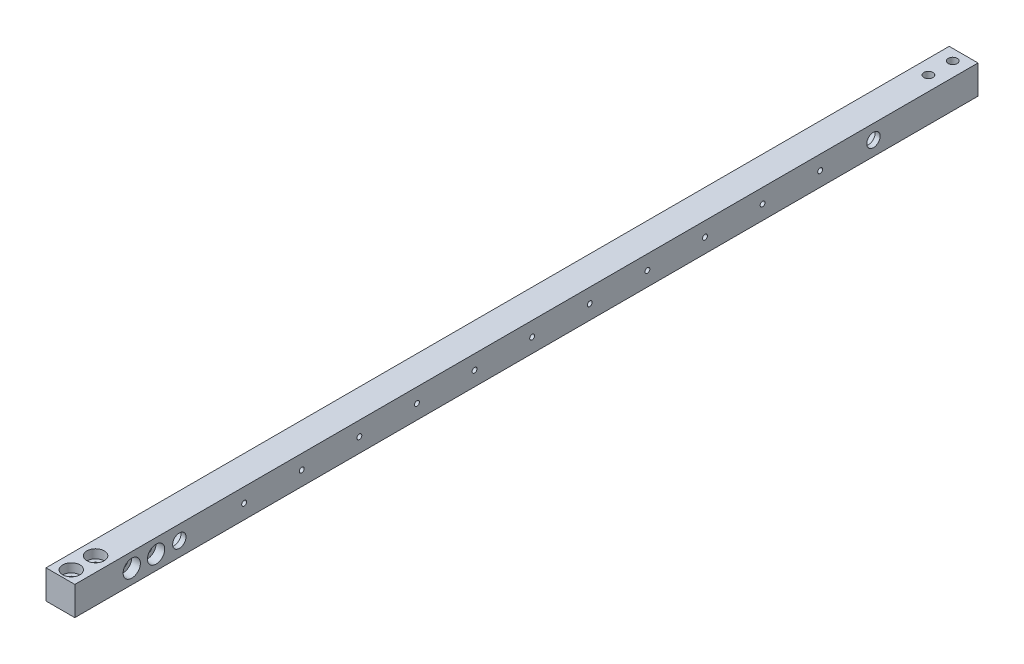
SolidWorks part; units mm, degrees
ref_plane "Front Plane" through (0, 0, 0) normal (0, 0, 1) x (1, 0, 0)
ref_plane "Top Plane" through (0, 0, 0) normal (0, 1, 0) x (1, 0, 0)
ref_plane "Right Plane" through (0, 0, 0) normal (1, 0, 0) x (0, 0, -1)
sketch "Sketch1" plane through (0, 0, 0) normal (0, 0, 1) x (1, 0, 0)
  line L1 (0, 0) -> (15.875, 0)
  line L2 (0, 0) -> (0, 15.875)
  line L3 (0, 15.875) -> (15.875, 15.875)
  line L4 (15.875, 0) -> (15.875, 15.875)
  dimension "D1" = 15.875
  dimension "D2" = 15.875
extrude "Boss-Extrude1" add sketch "Sketch1" along normal blind 497.84
sketch "Sketch8" plane through (0, 0, 0) normal (-1, 0, 0) x (0, 0, 1)
  line L0 (0, 15.875) -> (0, 0) construction
  line L1 (497.84, 15.875) -> (497.84, 0) construction
  circle A0 centre (440.2201, 7.9375) radius 6.8199
  circle A1 centre (57.6199, 7.9375) radius 6.8199
  point P2 (497.84, 7.9375)
  dimension "D1" = 57.6199
  dimension "D2" = 57.6199
extrude "Cut-Extrude1" cut sketch "Sketch8" against normal blind 13.0886
hole_wizard "L (0.29) Diameter Hole1" positions "Sketch10" profile "Sketch9" hole size "L" standard "ANSI Inch"
sketch "Sketch10" plane through (13.0886, 0, 0) normal (-1, 0, 0) x (0, 0, 1)
  point P0 (57.6199, 7.9375)
  point P3 (440.2201, 7.9375)
sketch "Sketch9" plane through (13.0886, 7.9375, 57.6199) normal (0, 1, 0) x (0, 0, 1)
  line L0 (0, 0) -> (0, 53.013)
  line L1 (0, 53.013) -> (3.683, 50.8)
  line L2 (3.683, 50.8) -> (3.683, 0)
  line L5 (3.683, 0) -> (0, 0)
  line L10 (0, 53.013) -> (-3.683, 50.8) construction
  line L11 (0, -6.35) -> (0, 107.95) construction
  dimension "Hole Dia." = 7.366
  dimension "Hole Depth" = 50.8
  dimension "Drill Angle" = 118
hole_wizard "Tap Drill for #6-32 Tap1" positions "Sketch17" profile "Sketch18" hole size "#6-32" standard "ANSI Inch" end condition through all
sketch "Sketch17" plane through (17.4625, -1824.3692, -1707.9731) normal (1, 0, 0) x (0, 0, -1)
  line L0 (-1794.9681, 1832.3067) -> (-2112.4681, 1832.3067) construction
  line L2 (-2205.8131, 1824.3692) -> (-1707.9731, 1824.3692) construction
  point P3 (-2112.4681, 1832.3067)
  point P6 (-2080.7181, 1832.3067)
  point P9 (-2048.9681, 1832.3067)
  point P12 (-2017.2181, 1832.3067)
  point P15 (-1985.4681, 1832.3067)
  point P18 (-1953.7181, 1832.3067)
  point P21 (-1921.9681, 1832.3067)
  point P24 (-1890.2181, 1832.3067)
  point P27 (-1858.4681, 1832.3067)
  point P30 (-1826.7181, 1832.3067)
  point P33 (-1794.9681, 1832.3067)
  dimension "D1" = 7.9375
sketch "Sketch18" plane through (17.4625, 7.9375, 404.495) normal (0, 1, 0) x (0, 0, -1)
  line L0 (0, 0) -> (0, 17.4625)
  line L1 (0, 17.4625) -> (1.3525, 17.4625)
  line L2 (1.3525, 17.4625) -> (1.3525, 0)
  line L3 (1.3525, 0) -> (0, 0)
  line L4 (0, -6.35) -> (0, 107.95) construction
  dimension "Thru Hole Dia." = 2.7051
  dimension "Thru Hole Depth" = 17.4625
hole_wizard "CBORE for #10 Socket Head Cap Screw3" positions "Sketch19" profile "Sketch20" counterbore size "#10" standard "ANSI Inch"
sketch "Sketch19" plane through (-863.7241, 15.875, -1707.9731) normal (0, 1, 0) x (1, 0, 0)
  point P0 (871.6616, -2186.4131)
  point P3 (871.6616, -2199.8131)
  point P6 (404.9366, -2186.4131)
  point P9 (404.9366, -2199.8131)
sketch "Sketch20" plane through (7.9375, 15.875, 478.44) normal (1, 0, 0) x (0, 0, 1)
  line L0 (0, 0) -> (0, 26.8957)
  line L1 (0, 26.8957) -> (2.4892, 25.4)
  line L2 (2.4892, 25.4) -> (2.4892, 4.826)
  line L3 (2.4892, 4.826) -> (4.7625, 4.826)
  line L4 (4.7625, 4.826) -> (4.7625, 0)
  line L5 (4.7625, 0) -> (0, 0)
  line L6 (0, 26.8957) -> (-2.4892, 25.4) construction
  line L7 (0, -6.35) -> (0, 107.95) construction
  dimension "Hole Dia." = 4.9784
  dimension "Hole Depth" = 25.4
  dimension "C'Bore Dia." = 9.525
  dimension "C'Bore Depth" = 4.826
  dimension "Drill Angle" = 118
hole_wizard "CBORE for #10 Socket Head Cap Screw2" positions "Sketch21" profile "Sketch22" counterbore size "#10" standard "ANSI Inch"
sketch "Sketch21" plane through (-863.7241, 0, -1707.9731) normal (0, -1, 0) x (-1, 0, 0)
  point P0 (-404.9366, -1727.3731)
  point P3 (-404.9366, -1713.9731)
  point P6 (-871.6616, -1727.3731)
  point P9 (-871.6616, -1713.9731)
sketch "Sketch22" plane through (-458.7875, 0, 19.4) normal (1, 0, 0) x (0, 0, -1)
  line L0 (0, 0) -> (0, 26.8957)
  line L1 (0, 26.8957) -> (2.4892, 25.4)
  line L2 (2.4892, 25.4) -> (2.4892, 4.826)
  line L3 (2.4892, 4.826) -> (4.7625, 4.826)
  line L4 (4.7625, 4.826) -> (4.7625, 0)
  line L5 (4.7625, 0) -> (0, 0)
  line L6 (0, 26.8957) -> (-2.4892, 25.4) construction
  line L7 (0, -6.35) -> (0, 107.95) construction
  dimension "Hole Dia." = 4.9784
  dimension "Hole Depth" = 25.4
  dimension "C'Bore Dia." = 9.525
  dimension "C'Bore Depth" = 4.826
  dimension "Drill Angle" = 118
hole_wizard "CBORE for #10 Socket Head Cap Screw1" positions "Sketch23" profile "Sketch24" counterbore size "#10" standard "ANSI Inch"
sketch "Sketch23" plane through (15.875, -1686.1795, -1707.9731) normal (1, 0, 0) x (0, 0, -1)
  point P0 (-2161.0131, 1694.117)
  point P3 (-2174.4131, 1694.117)
sketch "Sketch24" plane through (15.875, 7.9375, 453.04) normal (0, 1, 0) x (0, 0, -1)
  line L0 (0, 0) -> (0, 26.8957)
  line L1 (0, 26.8957) -> (2.4892, 25.4)
  line L2 (2.4892, 25.4) -> (2.4892, 4.826)
  line L3 (2.4892, 4.826) -> (4.7625, 4.826)
  line L4 (4.7625, 4.826) -> (4.7625, 0)
  line L5 (4.7625, 0) -> (0, 0)
  line L6 (0, 26.8957) -> (-2.4892, 25.4) construction
  line L7 (0, -6.35) -> (0, 107.95) construction
  dimension "Hole Dia." = 4.9784
  dimension "Hole Depth" = 25.4
  dimension "C'Bore Dia." = 9.525
  dimension "C'Bore Depth" = 4.826
  dimension "Drill Angle" = 118
